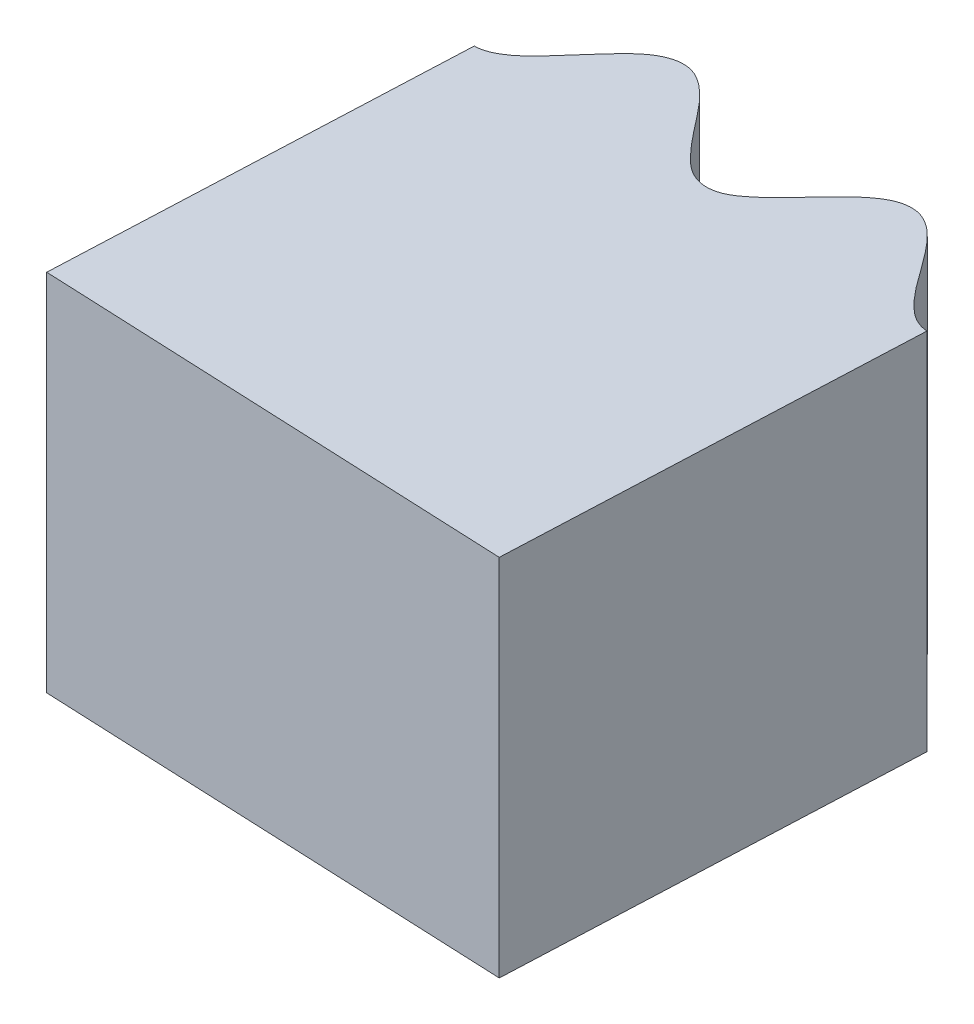
SolidWorks part; units mm, degrees
ref_plane "Front Plane" through (0, 0, 0) normal (0, 0, 1) x (1, 0, 0)
ref_plane "Top Plane" through (0, 0, 0) normal (0, 1, 0) x (1, 0, 0)
ref_plane "Right Plane" through (0, 0, 0) normal (1, 0, 0) x (0, 0, -1)
sketch "Sketch1" plane through (0, 0, 0) normal (0, 1, 0) x (1, 0, 0)
  line L0 (0, 75) -> (0, 70)
  line L1 (75, 0) -> (70, 0)
  arc A0 (0, 70) -> (70, 0) centre (0, 0) cw
  spline S0 degree 4 number of poles 795 (73.7726, -10.8158) -> (-10.9415, 74.6402) construction
  spline S1 degree 4 number of poles 661 (75, 0) -> (0, 75)
  dimension "D1" = 70
extrude "Boss-Extrude1" add sketch "Sketch1" along normal blind 4
sketch "Sketch2" plane through (0, 4, 0) normal (0, 1, 0) x (1, 0, 0)
  line L0 (0.6501, 74.4968) -> (0.4537, 69.9985)
  line L1 (0, 75) -> (0, 70) construction
  line L2 (0, 75) -> (0, 70)
  arc A0 (70, 0) -> (0, 70) centre (0, 0) ccw construction
  arc A2 (0.4537, 69.9985) -> (0, 70) centre (0, 0) ccw
  spline S0 degree 4 number of poles 661 (75, 0) -> (0, 75) construction
  point P2 (0, 0)
  point P3 (0, 0)
  point P7 (0.6501, 74.4968)
  dimension "D2" = 0.5
  dimension "D1" = 2.5
extrude "Cut-Extrude1" cut sketch "Sketch2" against normal through all both and the other way through all
sketch "Sketch3" plane through (0, 4, 0) normal (0, 1, 0) x (1, 0, 0)
  line L0 (5.6488, 69.7717) -> (5.8453, 74.2714)
  line L1 (0.4537, 69.9985) -> (0.6501, 74.4968) construction
  line L2 (70, 0) -> (75, 0) construction
  line L3 (70, 0) -> (75, 0)
  arc A0 (70, 0) -> (0.4537, 69.9985) centre (0, 0) ccw construction
  arc A1 (70, 0) -> (5.6488, 69.7717) centre (0, 0) ccw
  spline S0 degree 4 number of poles 658 (75, 0) -> (0.6501, 74.4968) construction
  point P5 (0, 0)
  point P7 (0, 0)
  point P8 (5.7943, 74.2787)
  dimension "D1" = 4
extrude "Cut-Extrude2" cut sketch "Sketch3" against normal through all both and the other way through all
sketch "Sketch4" plane through (0, 0, 0) normal (0, 1, 0) x (1, 0, 0)
  line L0 (0.4537, 69.9985) -> (5.6488, 69.7717)
  arc A0 (5.6488, 69.7717) -> (0.4537, 69.9985) centre (0, 0) ccw construction
  arc A1 (5.6488, 69.7717) -> (0.4537, 69.9985) centre (0, 0) ccw
extrude "Boss-Extrude2" add sketch "Sketch4" along normal up to surface (4 mm away) up to face at (3.7994, 4, -72.1185)
ref_plane "Plane1" through (0, 0, 0) normal (0.999, 0, 0.0436) x (0.0436, 0, -0.999)
